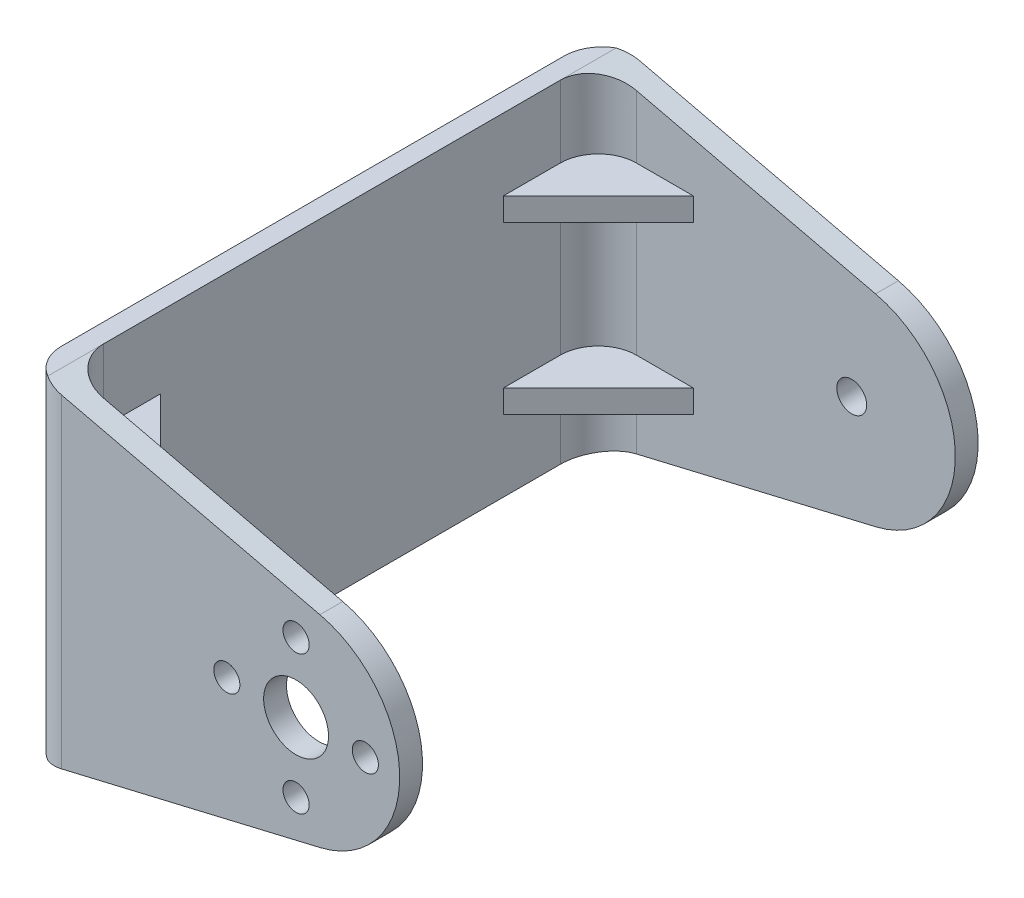
SolidWorks part; units mm, degrees
ref_plane "Front Plane" through (0, 0, 0) normal (0, 0, 1) x (1, 0, 0)
ref_plane "Top Plane" through (0, 0, 0) normal (0, 1, 0) x (1, 0, 0)
ref_plane "Right Plane" through (0, 0, 0) normal (1, 0, 0) x (0, 0, -1)
sketch "Sketch1" plane through (0, 0, 0) normal (0, 0, 1) x (1, 0, 0)
  line L0 (12.1275, -0.6077) -> (-17.03, -7.5)
  line L1 (-17.03, -7.5) -> (-17.03, 27.5)
  line L2 (-17.03, 27.5) -> (12.1275, 20.6077)
  line L3 (-17.03, 10) -> (-0.78, 10) construction
  line L4 (-0.4141, 34.143) -> (5.6286, 19.6036) construction
  arc A0 (12.1275, -0.6077) -> (12.1275, 20.6077) centre (9.62, 10) ccw
  circle A1 centre (9.62, 10) radius 10.4 construction
  point P11 (-17.03, 10)
  dimension "D1" = 0.5
  dimension "D2" = 35
  dimension "D3" = 16.25
  dimension "D4" = 15.7451
extrude "Boss-Extrude1" add sketch "Sketch1" along normal blind 2.4
ref_plane "Plane1" through (0, 0, -56.0482) normal (0, 0, -1) x (-1, 0, 0)
sketch "Sketch3" plane through (0, 0, -56.0482) normal (0, 0, -1) x (-1, 0, 0)
  line L15 (-12.1275, -0.6077) -> (17.03, -7.5)
  line L16 (17.03, 27.5) -> (-12.1275, 20.6077)
  line L17 (17.03, -7.5) -> (17.03, 27.5)
  line L18 (-12.1275, -0.6077) -> (17.03, -7.5)
  line L19 (17.03, 27.5) -> (-12.1275, 20.6077)
  line L20 (17.03, -7.5) -> (17.03, 27.5)
  arc A2 (-12.1275, 20.6077) -> (-12.1275, -0.6077) centre (-9.62, 10) ccw
  arc A3 (-12.1275, 20.6077) -> (-12.1275, -0.6077) centre (-9.62, 10) ccw
  dimension "D1" = 0
extrude "Boss-Extrude2" add sketch "Sketch3" along normal blind 2.4 separate body
sketch "Sketch2" plane through (0, 0, 2.4) normal (0, 0, 1) x (1, 0, 0)
  line L0 (-17.03, -7.5) -> (-17.03, 27.5)
  line L1 (-17.03, -7.5) -> (-19.03, -7.5)
  line L2 (-17.03, 27.5) -> (-19.03, 27.5)
  line L3 (-19.03, -7.5) -> (-19.03, 27.5)
  dimension "D1" = 2
extrude "Boss-Extrude3" add sketch "Sketch2" against normal up to surface (60.8482 mm away) up to face at (-0.3531, 10, -58.4482)
sketch "Sketch4" plane through (0, 0, -58.4482) normal (0, 0, -1) x (-1, 0, 0)
  circle A0 centre (-9.62, 10) radius 1.575
  arc A1 (-12.1275, 20.6077) -> (-12.1275, -0.6077) centre (-9.62, 10) ccw construction
  dimension "D1" = 3.15
extrude "Cut-Extrude1" cut sketch "Sketch4" against normal up to next
sketch "Sketch6" plane through (0, 0, 2.4) normal (0, 0, 1) x (1, 0, 0)
  circle A0 centre (9.62, 10) radius 3.41
  circle A1 centre (2.335, 10) radius 1.375
  circle A2 centre (2.335, 10) radius 0.875 construction
  circle A3 centre (9.62, 10) radius 2.91 construction
  circle A4 centre (9.62, 17.285) radius 1.375
  circle A5 centre (16.905, 10) radius 1.375
  circle A6 centre (9.62, 2.715) radius 1.375
  point P19 (9.62, 10)
  dimension "D1" = 0.5
  dimension "D2" = 0.5
  dimension "D3" = 4
extrude "Cut-Extrude2" cut sketch "Sketch6" against normal up to next
fillet "Fillet1" radius 4 4 edges at (-19.03, 10, -58.4482) (-19.03, 10, 2.4) (-17.03, 10, 0) (-17.03, 10, -56.0482)
ref_plane "Plane2" through (0, 10, 0) normal (0, -1, 0) x (-1, 0, 0)
ref_plane "Plane3" through (0, 1.25, 0) normal (0, -1, 0) x (-1, 0, 0)
ref_plane "Plane4" through (0, 18.75, 0) normal (0, -1, 0) x (-1, 0, 0)
sketch "Sketch9" plane through (0, 18.75, 0) normal (0, -1, 0) x (-1, 0, 0)
  line L0 (17.03, 46.0482) -> (7.03, 56.0482)
  line L1 (17.03, 52.0482) -> (17.03, 4) construction
  line L2 (-12.1275, 56.0482) -> (13.03, 56.0482) construction
  line L3 (7.03, 56.0482) -> (17.03, 56.0482)
  line L4 (17.03, 57.9123) -> (17.03, 52.0482) construction
  line L5 (17.03, 56.0482) -> (17.03, 46.0482)
  line L6 (17.03, 10) -> (17.03, 0)
  line L7 (17.03, -1.8641) -> (17.03, 4) construction
  line L8 (17.03, 0) -> (7.03, 0)
  line L9 (13.03, 0) -> (-12.1275, 0) construction
  line L10 (7.03, 0) -> (17.03, 10)
  dimension "D1" = 10
  dimension "D2" = 10
  dimension "D3" = 10
  dimension "D4" = 10
extrude "Boss-Extrude4" add sketch "Sketch9" along normal mid plane 2.4
sketch "Sketch10" plane through (0, 1.25, 0) normal (0, -1, 0) x (-1, 0, 0)
  line L1 (7.03, 56.0482) -> (17.03, 56.0482)
  line L2 (17.03, 57.9123) -> (17.03, 52.0482) construction
  line L3 (17.03, 56.0482) -> (17.03, 46.0482)
  line L4 (17.03, 46.0482) -> (7.03, 56.0482)
  line L5 (17.03, 10) -> (17.03, 0)
  line L6 (17.03, -1.8641) -> (17.03, 4) construction
  line L7 (17.03, 0) -> (7.03, 0)
  line L8 (7.03, 0) -> (17.03, 10)
extrude "Boss-Extrude5" add sketch "Sketch10" along normal mid plane 2.4
